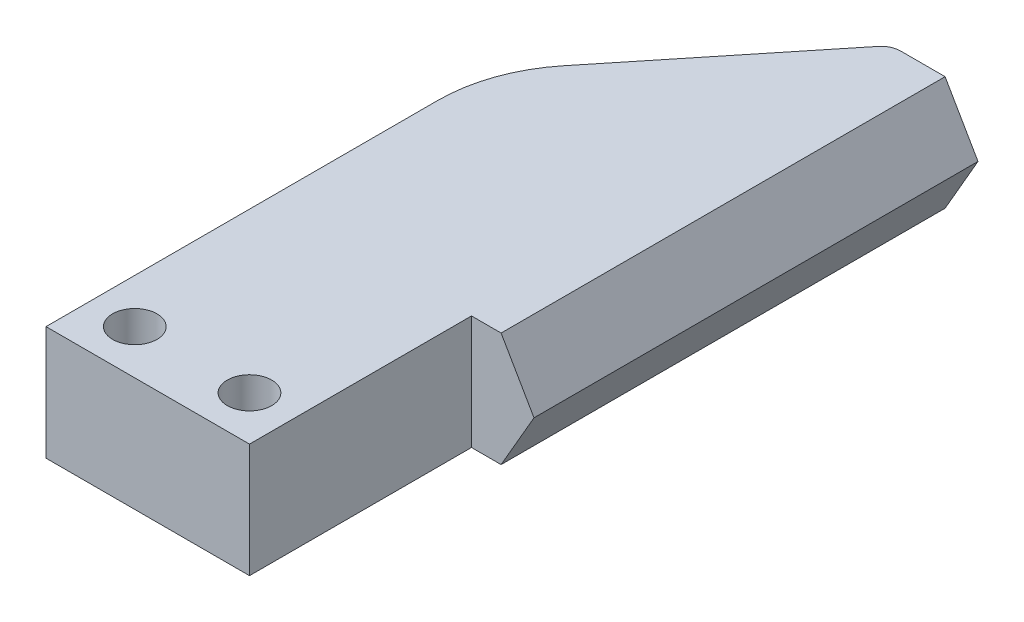
SolidWorks part; units mm, degrees
ref_plane "Front Plane" through (0, 0, 0) normal (0, 0, 1) x (1, 0, 0)
ref_plane "Top Plane" through (0, 0, 0) normal (0, 1, 0) x (1, 0, 0)
ref_plane "Right Plane" through (0, 0, 0) normal (1, 0, 0) x (0, 0, -1)
sketch "Sketch1" plane through (0, 0, 0) normal (0, 1, 0) x (1, 0, 0)
  line L0 (-13.75, -15) -> (0, -15)
  line L1 (-13.75, -15) -> (-13.75, 11.4669)
  line L6 (-6.875, -18.3439) -> (-6.875, -15) construction
  line L7 (0, 0) -> (0, -15)
  line L8 (-11.5305, 17.7489) -> (-2.0401, 29.503)
  line L11 (2, 30) -> (2, 0)
  line L12 (2, 0) -> (0, 0)
  line L13 (-1, 30) -> (2, 30)
  arc A1 (-2.0401, 29.503) -> (-1, 30) centre (-1, 28.6632) cw
  circle A3 centre (-10.75, -12) radius 1.5
  circle A5 centre (-3, -12) radius 1.5
  arc A6 (-13.75, 11.4669) -> (-11.5305, 17.7489) centre (-3.75, 11.4669) cw
  point P15 (-13.75, 15)
  dimension "D2" = 3
  dimension "D6" = 1.3368
  dimension "D10" = 3
  dimension "D12" = 3
  dimension "D13" = 10
  dimension "D3" = 13.75
  dimension "D4" = 18.6403
  dimension "D5" = 30
  dimension "D7" = 30
  dimension "D8" = 15
  dimension "D9" = 2
  dimension "D11" = 3
  dimension "D14" = 7.75
extrude "Boss-Extrude3" add sketch "Sketch1" along normal mid plane 7.7
sketch "Sketch2" plane through (0, 0, -30) normal (0, 0, -1) x (-1, 0, 0)
  line L0 (-2, 3.85) -> (-4.2228, 0)
  line L1 (-4.2228, 0) -> (-2, -3.85)
  line L2 (-2, -3.85) -> (-2, 3.85)
  line L3 (13.75, 0) -> (-17.0272, 0) construction
  line L4 (13.75, 3.85) -> (13.75, -3.85) construction
  dimension "D1" = 120
extrude "Boss-Extrude4" add sketch "Sketch2" against normal blind 30
